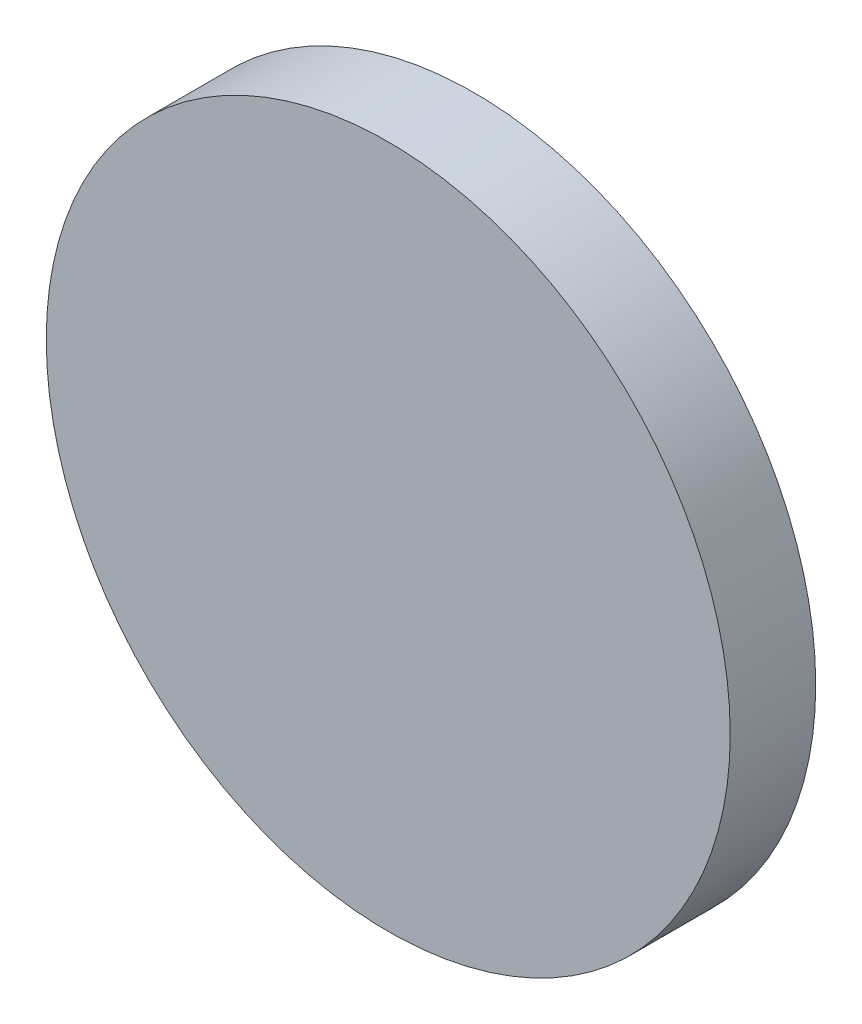
SolidWorks part; units mm, degrees
ref_plane "Ebene vorne" through (0, 0, 0) normal (0, 0, 1) x (1, 0, 0)
ref_plane "Ebene oben" through (0, 0, 0) normal (0, 1, 0) x (1, 0, 0)
ref_plane "Ebene rechts" through (0, 0, 0) normal (1, 0, 0) x (0, 0, -1)
sketch "Skizze1" plane through (0, 0, 0) normal (0, 0, 1) x (1, 0, 0)
  circle A0 centre (0, 0) radius 40
  dimension "D1" = 80
extrude "Aufsatz-Linear austragen1" add sketch "Skizze1" along normal blind 10 contours A0
sketch "Skizze2" plane through (0, 0, 10) normal (0, 0, 1) x (1, 0, 0)
  circle A0 centre (0, 0) radius 5
curve "Spirale/Helix1"
sketch "Skizze3" plane through (0, 0, 10) normal (0, 0, 1) x (1, 0, 0)
  circle A0 centre (0, 0) radius 5
curve "Spirale/Helix2"
